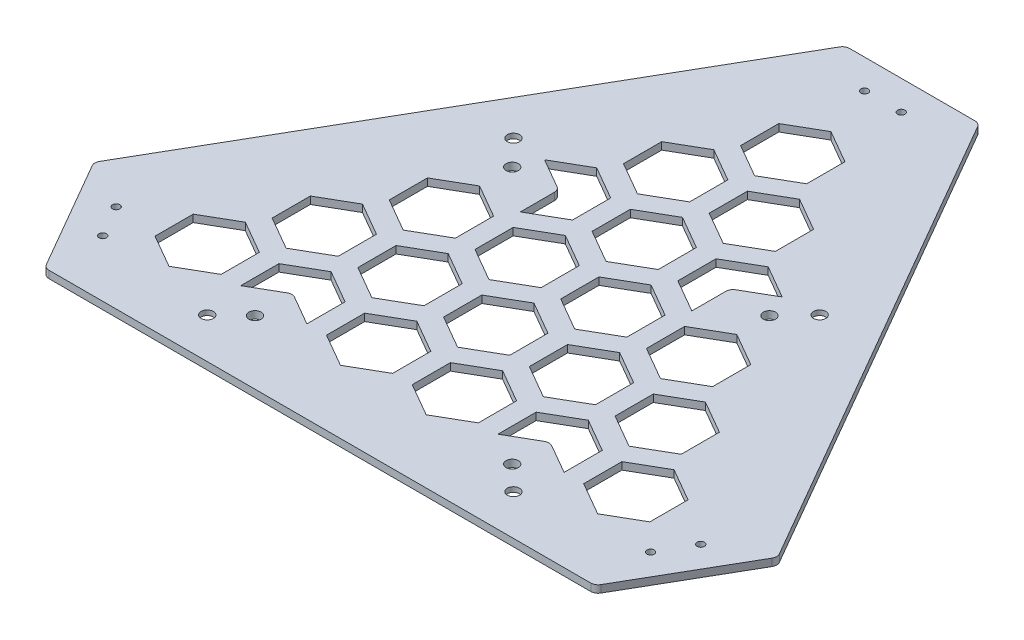
SolidWorks part; units mm, degrees
ref_plane "前基準面" through (0, 0, 0) normal (0, 0, 1) x (1, 0, 0)
ref_plane "上基準面" through (0, 0, 0) normal (0, 1, 0) x (1, 0, 0)
ref_plane "右基準面" through (0, 0, 0) normal (1, 0, 0) x (0, 0, -1)
ref_plane "平面1" through (0, -3, 0) normal (0, -1, 0) x (1, 0, 0)
sketch "草圖1" plane through (0, -3, 0) normal (0, -1, 0) x (1, 0, 0)
  line L0 (28.1754, -143.9508) -> (138.7528, 47.5748)
  line L1 (138.7528, 50.5748) -> (113.1754, 94.876)
  line L2 (110.5774, 96.376) -> (-110.5774, 96.376)
  line L3 (-113.1754, 94.876) -> (-138.7528, 50.5748)
  line L4 (-138.7528, 47.5748) -> (-28.1754, -143.9508)
  line L5 (-25.5774, -145.4508) -> (25.5774, -145.4508)
  arc A0 (138.7528, 47.5748) -> (138.7528, 50.5748) centre (136.1547, 49.0748) ccw
  arc A1 (113.1754, 94.876) -> (110.5774, 96.376) centre (110.5774, 93.376) ccw
  arc A2 (-110.5774, 96.376) -> (-113.1754, 94.876) centre (-110.5774, 93.376) ccw
  arc A3 (-138.7528, 50.5748) -> (-138.7528, 47.5748) centre (-136.1547, 49.0748) ccw
  arc A4 (-28.1754, -143.9508) -> (-25.5774, -145.4508) centre (-25.5774, -142.4508) ccw
  arc A5 (25.5774, -145.4508) -> (28.1754, -143.9508) centre (25.5774, -142.4508) ccw
extrude "填料-伸長1" add sketch "草圖1" against normal blind 3
sketch "草圖2" plane through (0, -3, 0) normal (0, -1, 0) x (1, 0, 0)
  line L0 (21.5, 16.7942) -> (35, 9)
  line L1 (35, 9) -> (48.5, 16.7942)
  line L2 (48.5, 16.7942) -> (48.5, 32.3827)
  line L3 (48.5, 32.3827) -> (35, 40.1769)
  line L4 (35, 40.1769) -> (21.5, 32.3827)
  line L5 (21.5, 32.3827) -> (21.5, 16.7942)
extrude "除料-伸長1" cut sketch "草圖2" against normal through all
sketch "草圖3" plane through (0, -3, 0) normal (0, -1, 0) x (1, 0, 0)
  line L0 (-48.5, -43.8275) -> (-35, -51.6218)
  line L1 (-35, -51.6218) -> (-21.5, -43.8275)
  line L2 (-21.5, -43.8275) -> (-21.5, -28.2391)
  line L3 (-21.5, -28.2391) -> (-35, -20.4449)
  line L4 (-35, -20.4449) -> (-35, -34.3013)
  line L5 (-36.5, -36.8993) -> (-48.5, -43.8275)
  arc A0 (-35, -34.3013) -> (-36.5, -36.8993) centre (-38, -34.3013) cw
extrude "除料-伸長2" cut sketch "草圖3" against normal through all
sketch "草圖4" plane through (0, -3, 0) normal (0, -1, 0) x (1, 0, 0)
  line L0 (-13.5, -43.8275) -> (0, -51.6218)
  line L1 (0, -51.6218) -> (13.5, -43.8275)
  line L2 (13.5, -43.8275) -> (13.5, -28.2391)
  line L3 (13.5, -28.2391) -> (0, -20.4449)
  line L4 (0, -20.4449) -> (-13.5, -28.2391)
  line L5 (-13.5, -28.2391) -> (-13.5, -43.8275)
extrude "除料-伸長3" cut sketch "草圖4" against normal through all
sketch "草圖5" plane through (0, -3, 0) normal (0, -1, 0) x (1, 0, 0)
  line L0 (39, -13.5167) -> (52.5, -21.3109)
  line L1 (52.5, -21.3109) -> (66, -13.5167)
  line L2 (66, -13.5167) -> (66, 2.0718)
  line L3 (66, 2.0718) -> (52.5, 9.866)
  line L4 (52.5, 9.866) -> (39, 2.0718)
  line L5 (39, 2.0718) -> (39, -13.5167)
extrude "除料-伸長4" cut sketch "草圖5" against normal through all
sketch "草圖6" plane through (0, -3, 0) normal (0, -1, 0) x (1, 0, 0)
  line L0 (4, -74.1384) -> (17.5, -81.9327)
  line L1 (17.5, -81.9327) -> (31, -74.1384)
  line L2 (31, -74.1384) -> (31, -58.55)
  line L3 (31, -58.55) -> (17.5, -50.7558)
  line L4 (17.5, -50.7558) -> (4, -58.55)
  line L5 (4, -58.55) -> (4, -74.1384)
extrude "除料-伸長5" cut sketch "草圖6" against normal through all
sketch "草圖7" plane through (0, -3, 0) normal (0, -1, 0) x (1, 0, 0)
  line L0 (-31, -74.1384) -> (-17.5, -81.9327)
  line L1 (-17.5, -81.9327) -> (-4, -74.1384)
  line L2 (-4, -74.1384) -> (-4, -58.55)
  line L3 (-4, -58.55) -> (-17.5, -50.7558)
  line L4 (-17.5, -50.7558) -> (-31, -58.55)
  line L5 (-31, -58.55) -> (-31, -74.1384)
extrude "除料-伸長6" cut sketch "草圖7" against normal through all
sketch "草圖8" plane through (0, -3, 0) normal (0, -1, 0) x (1, 0, 0)
  line L0 (4, -13.5167) -> (17.5, -21.3109)
  line L1 (17.5, -21.3109) -> (31, -13.5167)
  line L2 (31, -13.5167) -> (31, 2.0718)
  line L3 (31, 2.0718) -> (17.5, 9.866)
  line L4 (17.5, 9.866) -> (4, 2.0718)
  line L5 (4, 2.0718) -> (4, -13.5167)
extrude "除料-伸長7" cut sketch "草圖8" against normal through all
sketch "草圖9" plane through (0, -3, 0) normal (0, -1, 0) x (1, 0, 0)
  line L0 (56.5, 16.7942) -> (70, 9)
  line L1 (70, 9) -> (83.5, 16.7942)
  line L2 (83.5, 16.7942) -> (83.5, 32.3827)
  line L3 (83.5, 32.3827) -> (70, 40.1769)
  line L4 (70, 40.1769) -> (56.5, 32.3827)
  line L5 (56.5, 32.3827) -> (56.5, 16.7942)
extrude "除料-伸長8" cut sketch "草圖9" against normal through all
sketch "草圖10" plane through (0, -3, 0) normal (0, -1, 0) x (1, 0, 0)
  line L0 (-13.5, 16.7942) -> (0, 9)
  line L1 (0, 9) -> (13.5, 16.7942)
  line L2 (13.5, 16.7942) -> (13.5, 32.3827)
  line L3 (13.5, 32.3827) -> (0, 40.1769)
  line L4 (0, 40.1769) -> (-13.5, 32.3827)
  line L5 (-13.5, 32.3827) -> (-13.5, 16.7942)
extrude "除料-伸長9" cut sketch "草圖10" against normal through all
sketch "草圖11" plane through (0, -3, 0) normal (0, -1, 0) x (1, 0, 0)
  line L0 (39, 62.6936) -> (39, 47.1051)
  line L1 (39, 47.1051) -> (52.5, 39.3109)
  line L2 (52.5, 39.3109) -> (66, 47.1051)
  line L3 (66, 47.1051) -> (66, 62.6936)
  line L4 (66, 62.6936) -> (54, 55.7654)
  line L5 (51, 55.7654) -> (39, 62.6936)
  arc A0 (54, 55.7654) -> (51, 55.7654) centre (52.5, 58.3634) cw
extrude "除料-伸長10" cut sketch "草圖11" against normal through all
sketch "草圖12" plane through (0, -3, 0) normal (0, -1, 0) x (1, 0, 0)
  line L0 (-48.5, 16.7942) -> (-35, 9)
  line L1 (-35, 9) -> (-21.5, 16.7942)
  line L2 (-21.5, 16.7942) -> (-21.5, 32.3827)
  line L3 (-21.5, 32.3827) -> (-35, 40.1769)
  line L4 (-35, 40.1769) -> (-48.5, 32.3827)
  line L5 (-48.5, 32.3827) -> (-48.5, 16.7942)
extrude "除料-伸長11" cut sketch "草圖12" against normal through all
sketch "草圖13" plane through (0, -3, 0) normal (0, -1, 0) x (1, 0, 0)
  line L0 (-83.5, 16.7942) -> (-70, 9)
  line L1 (-70, 9) -> (-56.5, 16.7942)
  line L2 (-56.5, 16.7942) -> (-56.5, 32.3827)
  line L3 (-56.5, 32.3827) -> (-70, 40.1769)
  line L4 (-70, 40.1769) -> (-83.5, 32.3827)
  line L5 (-83.5, 32.3827) -> (-83.5, 16.7942)
extrude "除料-伸長12" cut sketch "草圖13" against normal through all
sketch "草圖14" plane through (0, -3, 0) normal (0, -1, 0) x (1, 0, 0)
  line L0 (35, -20.4449) -> (21.5, -28.2391)
  line L1 (21.5, -28.2391) -> (21.5, -43.8275)
  line L2 (21.5, -43.8275) -> (35, -51.6218)
  line L3 (35, -51.6218) -> (48.5, -43.8275)
  line L4 (48.5, -43.8275) -> (36.5, -36.8993)
  line L5 (35, -34.3013) -> (35, -20.4449)
  arc A0 (36.5, -36.8993) -> (35, -34.3013) centre (38, -34.3013) cw
extrude "除料-伸長13" cut sketch "草圖14" against normal through all
sketch "草圖15" plane through (0, -3, 0) normal (0, -1, 0) x (1, 0, 0)
  line L0 (-66, -13.5167) -> (-52.5, -21.3109)
  line L1 (-52.5, -21.3109) -> (-39, -13.5167)
  line L2 (-39, -13.5167) -> (-39, 2.0718)
  line L3 (-39, 2.0718) -> (-52.5, 9.866)
  line L4 (-52.5, 9.866) -> (-66, 2.0718)
  line L5 (-66, 2.0718) -> (-66, -13.5167)
extrude "除料-伸長14" cut sketch "草圖15" against normal through all
sketch "草圖16" plane through (0, -3, 0) normal (0, -1, 0) x (1, 0, 0)
  line L0 (-31, -13.5167) -> (-17.5, -21.3109)
  line L1 (-17.5, -21.3109) -> (-4, -13.5167)
  line L2 (-4, -13.5167) -> (-4, 2.0718)
  line L3 (-4, 2.0718) -> (-17.5, 9.866)
  line L4 (-17.5, 9.866) -> (-31, 2.0718)
  line L5 (-31, 2.0718) -> (-31, -13.5167)
extrude "除料-伸長15" cut sketch "草圖16" against normal through all
sketch "草圖17" plane through (0, -3, 0) normal (0, -1, 0) x (1, 0, 0)
  line L0 (-101, 47.1051) -> (-87.5, 39.3109)
  line L1 (-87.5, 39.3109) -> (-74, 47.1051)
  line L2 (-74, 47.1051) -> (-74, 62.6936)
  line L3 (-74, 62.6936) -> (-87.5, 70.4878)
  line L4 (-87.5, 70.4878) -> (-101, 62.6936)
  line L5 (-101, 62.6936) -> (-101, 47.1051)
extrude "除料-伸長16" cut sketch "草圖17" against normal through all
sketch "草圖18" plane through (0, -3, 0) normal (0, -1, 0) x (1, 0, 0)
  line L0 (-31, 47.1051) -> (-17.5, 39.3109)
  line L1 (-17.5, 39.3109) -> (-4, 47.1051)
  line L2 (-4, 47.1051) -> (-4, 62.6936)
  line L3 (-4, 62.6936) -> (-17.5, 70.4878)
  line L4 (-17.5, 70.4878) -> (-31, 62.6936)
  line L5 (-31, 62.6936) -> (-31, 47.1051)
extrude "除料-伸長17" cut sketch "草圖18" against normal through all
sketch "草圖19" plane through (0, -3, 0) normal (0, -1, 0) x (1, 0, 0)
  line L0 (74, 47.1051) -> (87.5, 39.3109)
  line L1 (87.5, 39.3109) -> (101, 47.1051)
  line L2 (101, 47.1051) -> (101, 62.6936)
  line L3 (101, 62.6936) -> (87.5, 70.4878)
  line L4 (87.5, 70.4878) -> (74, 62.6936)
  line L5 (74, 62.6936) -> (74, 47.1051)
extrude "除料-伸長18" cut sketch "草圖19" against normal through all
sketch "草圖20" plane through (0, -3, 0) normal (0, -1, 0) x (1, 0, 0)
  line L0 (4, 47.1051) -> (17.5, 39.3109)
  line L1 (17.5, 39.3109) -> (31, 47.1051)
  line L2 (31, 47.1051) -> (31, 62.6936)
  line L3 (31, 62.6936) -> (17.5, 70.4878)
  line L4 (17.5, 70.4878) -> (4, 62.6936)
  line L5 (4, 62.6936) -> (4, 47.1051)
extrude "除料-伸長19" cut sketch "草圖20" against normal through all
sketch "草圖21" plane through (0, -3, 0) normal (0, -1, 0) x (1, 0, 0)
  line L0 (-13.5, -104.4493) -> (0, -112.2436)
  line L1 (0, -112.2436) -> (13.5, -104.4493)
  line L2 (13.5, -104.4493) -> (13.5, -88.8609)
  line L3 (13.5, -88.8609) -> (0, -81.0666)
  line L4 (0, -81.0666) -> (-13.5, -88.8609)
  line L5 (-13.5, -88.8609) -> (-13.5, -104.4493)
extrude "除料-伸長20" cut sketch "草圖21" against normal through all
sketch "草圖22" plane through (0, 0, 0) normal (0, 1, 0) x (-1, 0, 0)
  line L0 (39, 62.6936) -> (39, 47.1051)
  line L1 (39, 47.1051) -> (52.5, 39.3109)
  line L2 (52.5, 39.3109) -> (66, 47.1051)
  line L3 (66, 47.1051) -> (66, 62.6936)
  line L4 (66, 62.6936) -> (54, 55.7654)
  line L5 (51, 55.7654) -> (39, 62.6936)
  arc A0 (54, 55.7654) -> (51, 55.7654) centre (52.5, 58.3634) cw
extrude "除料-伸長21" cut sketch "草圖22" against normal through all
hole_wizard "鑽孔1" positions "草圖24" profile "草圖23" legacy
sketch "草圖24" plane through (0, -3, 0) normal (0, -1, 0) x (-1, 0, 0)
  point P0 (62.5, 45.124)
  point P1 (-62.5, 45.124)
  point P2 (-62.5, -79.876)
  point P3 (62.5, -79.876)
sketch "草圖23" plane through (-62.5, -3, -45.124) normal (1, 0, 0) x (0, 0, -1)
  line L0 (0, 0) -> (0, 3)
  line L1 (0, 3) -> (2.5, 3)
  line L2 (2.5, 3) -> (2.5, 1)
  line L3 (2.5, 1) -> (5.5, 1)
  line L4 (5.5, 1) -> (5.5, 0)
  line L5 (5.5, 0) -> (0, 0)
  line L6 (0, 110) -> (0, -10) construction
  dimension " 畖" = 5
  dimension "瞏 " = 3
  dimension "琖ふ 畖1" = 11
  dimension "琖ふ瞏 1" = 1
hole_wizard "Ø3.0 (3) 直徑孔1" positions "草圖26" profile "草圖25" hole size "Ø3.0" standard "Ansi Metric"
sketch "草圖26" plane through (0, 0, 0) normal (0, 1, 0) x (1, 0, 0)
  point P0 (111.8218, -73.2206)
  point P1 (119.3218, -60.2302)
  point P2 (7.5, 133.4508)
  point P3 (-7.5, 133.4508)
  point P4 (-111.8218, -73.2206)
  point P5 (-119.3218, -60.2302)
sketch "草圖25" plane through (111.8218, 0, 73.2206) normal (1, 0, 0) x (0, 0, 1)
  line L0 (0, 0) -> (0, 3)
  line L1 (0, 3) -> (1.5, 3)
  line L2 (1.5, 3) -> (1.5, 0)
  line L5 (1.5, 0) -> (0, 0)
  line L11 (0, -6.35) -> (0, 107.95) construction
  dimension "砮 ふ 畖" = 3
  dimension "砮 ふ瞏 " = 3
hole_wizard "Ø5.0 (5) 直徑孔1" positions "草圖28" profile "草圖27" hole size "Ø5.0" standard "Ansi Metric"
sketch "草圖28" plane through (0, -3, 0) normal (0, -1, 0) x (-1, 0, 0)
  point P0 (52.5, 34.624)
  point P1 (-52.5, 34.624)
  point P2 (-52.5, -70.376)
  point P3 (52.5, -70.376)
sketch "草圖27" plane through (-52.5, -3, -34.624) normal (1, 0, 0) x (0, 0, -1)
  line L0 (0, 0) -> (0, 3)
  line L1 (0, 3) -> (2.5, 3)
  line L2 (2.5, 3) -> (2.5, 0)
  line L5 (2.5, 0) -> (0, 0)
  line L11 (0, -6.35) -> (0, 107.95) construction
  dimension "砮 ふ 畖" = 5
  dimension "砮 ふ瞏 " = 3
